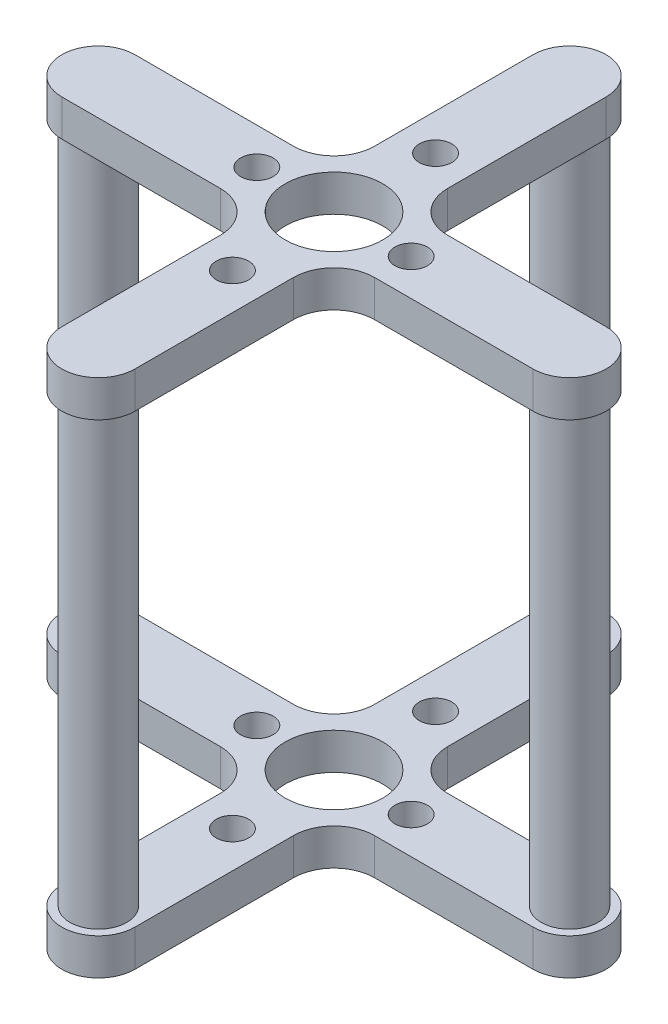
SolidWorks part; units mm, degrees
ref_plane "Front Plane" through (0, 0, 0) normal (0, 0, 1) x (1, 0, 0)
ref_plane "Top Plane" through (0, 0, 0) normal (0, 1, 0) x (1, 0, 0)
ref_plane "Right Plane" through (0, 0, 0) normal (1, 0, 0) x (0, 0, -1)
sketch "Sketch1" plane through (0, 0, 0) normal (0, 1, 0) x (1, 0, 0)
  line L0 (0, 29) -> (0, -29) construction
  line L1 (4.5, 29) -> (4.5, -29)
  line L2 (-4.5, 29) -> (-4.5, -29)
  line L3 (29, 0) -> (-29, 0) construction
  line L4 (29, -4.5) -> (-29, -4.5)
  line L5 (29, 4.5) -> (-29, 4.5)
  arc A0 (4.5, 29) -> (-4.5, 29) centre (0, 29) ccw
  arc A1 (-4.5, -29) -> (4.5, -29) centre (0, -29) ccw
  arc A2 (29, -4.5) -> (29, 4.5) centre (29, 0) ccw
  arc A3 (-29, 4.5) -> (-29, -4.5) centre (-29, 0) ccw
  point P2 (0, 0)
  point P13 (0, 0)
  point P18 (0, 0)
  dimension "D2" = 4.5
  dimension "D1" = 58
  dimension "D3" = 2
extrude "Boss-Extrude1" add sketch "Sketch1" along normal blind 4.5 contours L5 A3 L4 L2 | L4 A2 L5 L1
sketch "Sketch2" plane through (0, 4.5, 0) normal (0, 1, 0) x (1, 0, 0)
  line L0 (0, 0) -> (-16.2785, 0) construction
  line L1 (0, 0) -> (0, 10.6488) construction
  circle A0 centre (0, 0) radius 6
  circle A1 centre (9.5, 0) radius 2
  circle A2 centre (29, 0) radius 3.5
  circle A3 centre (0, 12.5) radius 2
  circle A4 centre (0, -29) radius 3.5
  circle A5 centre (-29, 0) radius 3.5
  circle A6 centre (0, 29) radius 3.5
  circle A7 centre (-9.5, 0) radius 2
  circle A8 centre (0, -12.5) radius 2
  point P19 (0, 0)
  dimension "D1" = 12
  dimension "D2" = 4
  dimension "D3" = 7
  dimension "D4" = 4
  dimension "D5" = 9.5
  dimension "D6" = 12.5
  dimension "D7" = 4
extrude "Cut-Extrude1" cut sketch "Sketch2" against normal through all
fillet "Fillet1" radius 5 4 edges at (-4.5, 2.25, 4.5) (4.5, 2.25, 4.5) (4.5, 2.25, -4.5) (-4.5, 2.25, -4.5)
sketch "Sketch4" plane through (0, 0, 0) normal (0, -1, 0) x (1, 0, 0)
  circle A0 centre (0, -29) radius 3.5
  circle A1 centre (-29, 0) radius 3.5
  circle A2 centre (0, 29) radius 3.5
  circle A3 centre (29, 0) radius 3.5
  point P12 (0, 0)
  dimension "D1" = 7
  dimension "D2" = 4
extrude "Boss-Extrude2" add sketch "Sketch4" along normal blind 27.5 and the other way blind 4.5
ref_plane "Plane1" through (0, -25, 0) normal (0, 1, 0) x (1, 0, 0)
mirror "Mirror2" about plane through (0, -27.5, 29) normal (0, -1, 0) of bodies 103
